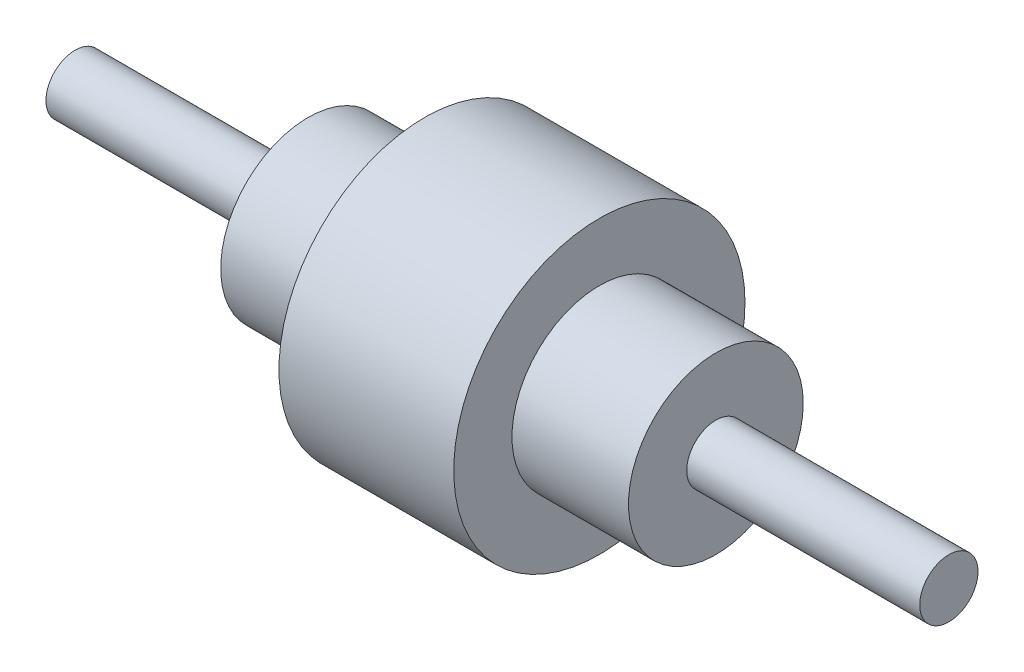
SolidWorks part; units mm, degrees
ref_plane "Front Plane" through (0, 0, 0) normal (0, 0, 1) x (1, 0, 0)
ref_plane "Top Plane" through (0, 0, 0) normal (0, 1, 0) x (1, 0, 0)
ref_plane "Right Plane" through (0, 0, 0) normal (1, 0, 0) x (0, 0, -1)
sketch "Sketch2" plane through (0, 0, 0) normal (0, 1, 0) x (1, 0, 0)
  line L0 (0, 0) -> (263.9376, 0) construction
  line L1 (0, 0) -> (-178.3753, 0) construction
  line L2 (45.0114, -30) -> (45.0114, -50)
  line L3 (45.0114, -50) -> (105.0114, -50)
  line L4 (105.0114, -50) -> (105.0114, -30)
  line L5 (105.0114, -30) -> (145.0114, -30)
  line L6 (145.0114, -30) -> (145.0114, -10)
  line L7 (145.0114, -10) -> (225.0114, -10)
  line L8 (225.0114, -10) -> (225.0114, 0)
  line L9 (45.0114, -30) -> (5.0114, -30)
  line L10 (5.0114, -30) -> (5.0114, -10)
  line L11 (5.0114, -10) -> (-74.9886, -10)
  line L12 (-74.9886, -10) -> (-74.9886, 0)
  line L13 (-74.9886, 0) -> (225.0114, 0)
  dimension "D1" = 60
  dimension "D2" = 40
  dimension "D3" = 80
  dimension "D4" = 40
  dimension "D5" = 80
  dimension "D6" = 100
  dimension "D7" = 20
  dimension "D8" = 60
  dimension "D9" = 40
  dimension "D10" = 20
  dimension "D11" = 60
  dimension "D12" = 100
  dimension "D13" = 225.0114
revolve "Revolve1" add sketch "Sketch2" angle 360 about L1
